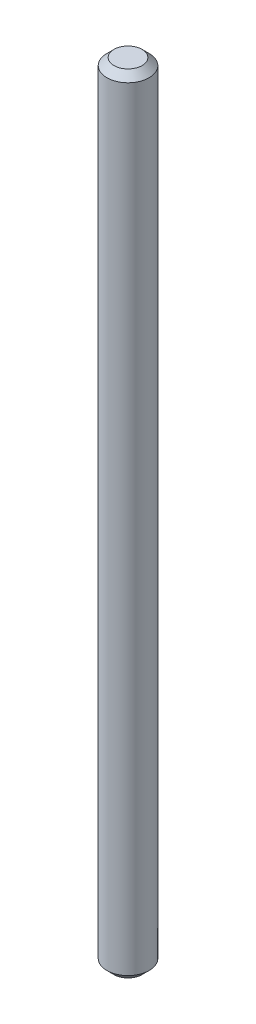
SolidWorks part; units mm, degrees
ref_plane "Front Plane" through (0, 0, 0) normal (0, 0, 1) x (1, 0, 0)
ref_plane "Top Plane" through (0, 0, 0) normal (0, 1, 0) x (1, 0, 0)
ref_plane "Right Plane" through (0, 0, 0) normal (1, 0, 0) x (0, 0, -1)
sketch "Sketch1" plane through (0, 0, 0) normal (0, 0, 1) x (1, 0, 0)
  line L0 (1, 5) -> (1.5, 4.5)
  line L1 (0, 5) -> (1, 5)
  line L2 (0, 5) -> (0, -51)
  line L3 (0, -51) -> (1, -51)
  line L4 (1.5, 4.5) -> (1.5, -50.5)
  line L5 (1.5, -50.5) -> (1, -51)
  line L6 (0, 5) -> (0, 61) construction
  dimension "D1" = 5
  dimension "D2" = 0.5
  dimension "D3" = 0.5
  dimension "D4" = 3
  dimension "D5" = 56
revolve "Revolve1" add sketch "Sketch1" angle 360 about L6
cosmetic thread "Cosmetic Thread1"
